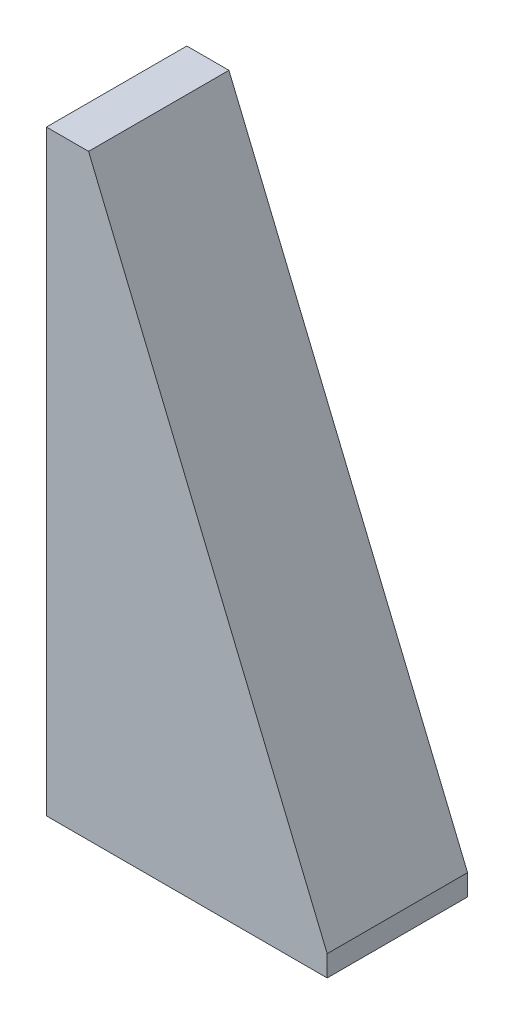
SolidWorks part; units mm, degrees
ref_plane "Front Plane" through (0, 0, 0) normal (0, 0, 1) x (1, 0, 0)
ref_plane "Top Plane" through (0, 0, 0) normal (0, 1, 0) x (1, 0, 0)
ref_plane "Right Plane" through (0, 0, 0) normal (1, 0, 0) x (0, 0, -1)
sketch "Sketch1" plane through (0, 0, 0) normal (0, 0, 1) x (1, 0, 0)
  line L0 (0, 0) -> (0, 41)
  line L1 (0, 41) -> (3, 41)
  line L2 (3, 41) -> (20, 0)
  line L3 (20, 0) -> (0, 0)
  dimension "D1" = 3
  dimension "D2" = 41
  dimension "D3" = 20
extrude "Boss-Extrude1" add sketch "Sketch1" along normal blind 10
sketch "Sketch2" plane through (0, 0, 10) normal (0, 0, 1) x (1, 0, 0)
  line L0 (0, 0) -> (20, 0)
  line L1 (20, 0) -> (20, -1.5)
  line L2 (20, -1.5) -> (0, -1.5)
  line L3 (0, -1.5) -> (0, 0)
  dimension "D1" = 1.5
extrude "Boss-Extrude2" add sketch "Sketch2" against normal up to surface (10 mm away) up to face at (5.75, 20.5, 0)
